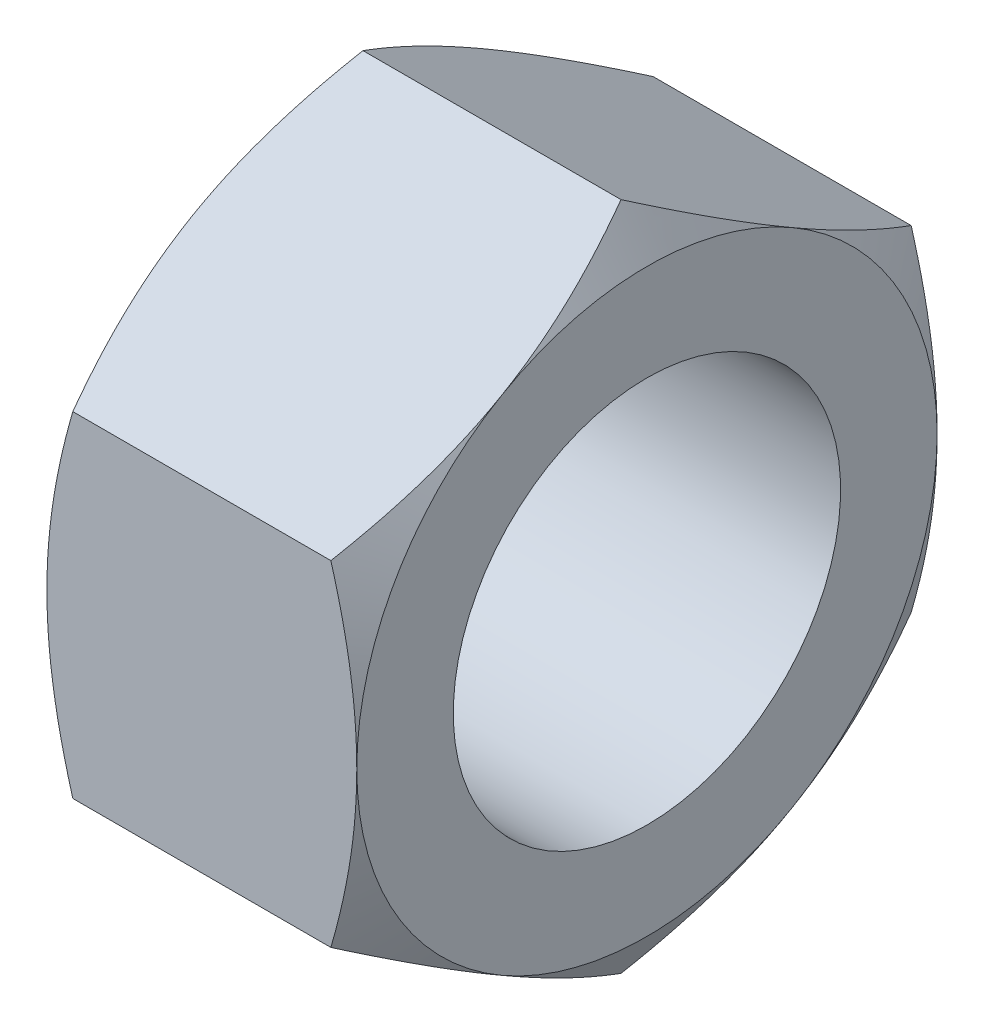
SolidWorks part; units mm, degrees
material "1.5714 (16NiCr4)"
ref_plane "Alzado" through (0, 0, 0) normal (0, 0, 1) x (1, 0, 0)
ref_plane "Planta" through (0, 0, 0) normal (0, 1, 0) x (1, 0, 0)
ref_plane "Vista lateral" through (0, 0, 0) normal (1, 0, 0) x (0, 0, -1)
sketch "Croquis1" plane through (0, 0, 0) normal (0, 0, 1) x (1, 0, 0)
  line L2 (0, 0) -> (0, 6.92)
  line L3 (0, 6.92) -> (6.4, 6.92)
  line L4 (6.4, 6.92) -> (6.4, 0)
  line L5 (6.4, 0) -> (0, 0)
  dimension "D3" = 6.92
  dimension "D4" = 6.4
revolve "Revolución1" add sketch "Croquis1" angle 360 about L5
sketch "Croquis2" plane through (6.4, 0, 0) normal (1, 0, 0) x (0, 0, -1)
  line L0 (0, 0) -> (0, 10.7677) construction
  line L1 (0, 6.92) -> (-5.9929, 3.46)
  line L2 (-5.9929, 3.46) -> (-5.9929, -3.46)
  line L3 (-5.9929, -3.46) -> (0, -6.92)
  line L4 (0, -6.92) -> (5.9929, -3.46)
  line L5 (5.9929, -3.46) -> (5.9929, 3.46)
  line L6 (5.9929, 3.46) -> (0, 6.92)
  circle A0 centre (0, 0) radius 5.9929 construction
  point P11 (0, 6.92)
  circle M7 centre (0, 0) radius 6.92
  dimension "D1" = 11.9858
extrude "Cortar-Extruir1" cut sketch "Croquis2" against normal blind 7 contours L2 M7 | L1 M7 | L6 M7 | L5 M7 | L4 M7 | L3 M7
sketch "Croquis3" plane through (6.4, 0, 0) normal (1, 0, 0) x (0, 0, -1)
  circle A0 centre (0, 0) radius 5.9929
  dimension "D1" = 11.9858
extrude "Cortar-Extruir2" cut sketch "Croquis3" against normal blind 7 draft 60 flip side to cut
sketch "Croquis5" plane through (0, 0, 0) normal (-1, 0, 0) x (0, 0, 1)
  circle A0 centre (0, 0) radius 5.9929
  dimension "D1" = 11.9858
extrude "Cortar-Extruir3" cut sketch "Croquis5" against normal blind 1 draft 60 flip side to cut
sketch "Croquis6" plane through (6.4, 0, 0) normal (1, 0, 0) x (0, 0, -1)
  circle A0 centre (0, 0) radius 4
  dimension "D1" = 8
extrude "Cortar-Extruir4" cut sketch "Croquis6" against normal blind 7
